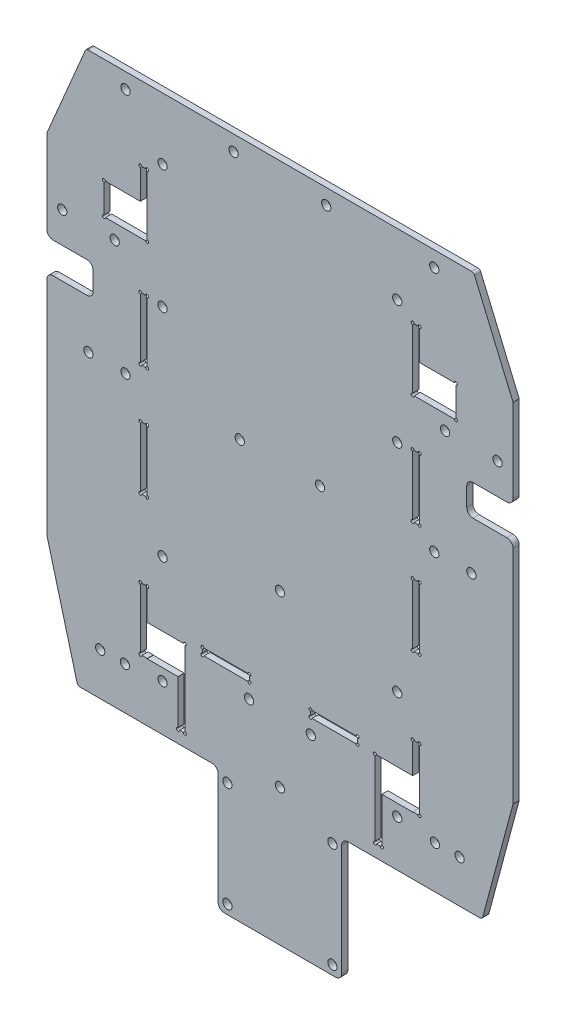
SolidWorks part; units mm, degrees
material "环氧板3240"
ref_plane "前视基准面" through (0, 0, 0) normal (0, 0, 1) x (1, 0, 0)
ref_plane "上视基准面" through (0, 0, 0) normal (0, 1, 0) x (1, 0, 0)
ref_plane "右视基准面" through (0, 0, 0) normal (1, 0, 0) x (0, 0, -1)
other "Configuration Table"
sketch "草图1" plane through (0, 0, 0) normal (0, 0, 1) x (1, 0, 0)
  line L0 (0, 90) -> (0, -90) construction
  line L2 (-43, 45.8) -> (-43, 30.5) construction
  line L3 (62.7658, 90) -> (-62.7658, 90)
  line L4 (75.5, 60) -> (75.5, -52.6795)
  line L5 (65.5, -90) -> (-65.5, -90)
  line L6 (-75.5, 60) -> (-75.5, -52.6795)
  line L7 (75.5, 90) -> (-75.5, -90) construction
  line L8 (75.5, -90) -> (-75.5, 90) construction
  line L9 (-43, 66) -> (-45.2, 66)
  line L10 (-43, 66) -> (-43, 45.8)
  line L11 (-43, 45.8) -> (-45.2, 45.8)
  line L12 (-45.2, 66) -> (-45.2, 45.8)
  line L13 (-43, 66) -> (-45.2, 45.8) construction
  line L14 (-43, 45.8) -> (-45.2, 66) construction
  line L15 (-43, 30.5) -> (-45.2, 30.5)
  line L16 (-43, 30.5) -> (-43, 10.3)
  line L17 (-43, 10.3) -> (-45.2, 10.3)
  line L18 (-45.2, 30.5) -> (-45.2, 10.3)
  line L19 (-43, 30.5) -> (-45.2, 10.3) construction
  line L20 (-43, 10.3) -> (-45.2, 30.5) construction
  line L21 (-43, -5.7) -> (-45.2, -5.7)
  line L22 (-43, -5.7) -> (-43, -25.9)
  line L23 (-43, -25.9) -> (-45.2, -25.9)
  line L24 (-45.2, -5.7) -> (-45.2, -25.9)
  line L25 (-43, -5.7) -> (-45.2, -25.9) construction
  line L26 (-43, -25.9) -> (-45.2, -5.7) construction
  line L27 (-43, 10.3) -> (-43, -5.7) construction
  line L28 (-50, 85) -> (-50, -54.1) construction
  line L33 (-50, -54.1) -> (50, -54.1) construction
  line L34 (50, -54.1) -> (50, 85) construction
  line L39 (43, -25.9) -> (45.2, -25.9)
  line L40 (45.2, -5.7) -> (45.2, -25.9)
  line L41 (43, -5.7) -> (45.2, -5.7)
  line L42 (43, -5.7) -> (43, -25.9)
  line L43 (43, 10.3) -> (45.2, 10.3)
  line L44 (45.2, 30.5) -> (45.2, 10.3)
  line L45 (43, 30.5) -> (45.2, 30.5)
  line L46 (43, 30.5) -> (43, 10.3)
  line L47 (43, 45.8) -> (45.2, 45.8)
  line L48 (45.2, 66) -> (45.2, 45.8)
  line L49 (43, 66) -> (45.2, 66)
  line L50 (43, 66) -> (43, 45.8)
  line L51 (50, 85) -> (-50, 85) construction
  line L52 (-43, -25.9) -> (-43, -50.9) construction
  line L53 (43, -71.1) -> (45.2, -71.1)
  line L54 (-43, -50.9) -> (-45.2, -50.9)
  line L55 (-43, -50.9) -> (-43, -71.1)
  line L56 (-43, -71.1) -> (-45.2, -71.1)
  line L57 (-45.2, -50.9) -> (-45.2, -71.1)
  line L58 (-43, -50.9) -> (-45.2, -71.1) construction
  line L59 (-43, -71.1) -> (-45.2, -50.9) construction
  line L60 (45.2, -50.9) -> (45.2, -71.1)
  line L61 (43, -50.9) -> (45.2, -50.9)
  line L62 (43, -50.9) -> (43, -71.1)
  line L63 (62.7658, 90) -> (75.5, 60)
  line L64 (25.1, -59) -> (9.9, -59)
  line L65 (25.1, -59) -> (25.1, -61.2)
  line L66 (25.1, -61.2) -> (9.9, -61.2)
  line L67 (9.9, -59) -> (9.9, -61.2)
  line L68 (25.1, -59) -> (9.9, -61.2) construction
  line L69 (25.1, -61.2) -> (9.9, -59) construction
  line L74 (-62.7658, 90) -> (-75.5, 60)
  line L75 (75.5, 60) -> (75.5, 90) construction
  line L76 (-9.9, -59) -> (-25.1, -59)
  line L77 (-9.9, -59) -> (-9.9, -61.2)
  line L78 (-9.9, -61.2) -> (-25.1, -61.2)
  line L79 (-25.1, -59) -> (-25.1, -61.2)
  line L80 (-9.9, -59) -> (-25.1, -61.2) construction
  line L81 (-9.9, -61.2) -> (-25.1, -59) construction
  line L82 (75.5, 90) -> (62.7658, 90) construction
  line L83 (-62.7658, 90) -> (-75.5, 90) construction
  line L84 (-75.5, 90) -> (-75.5, 60) construction
  line L85 (75.5, -52.6795) -> (65.5, -90)
  line L86 (-75.5, -52.6795) -> (-65.5, -90)
  line L87 (75.5, -52.6795) -> (75.5, -90) construction
  line L88 (75.5, -90) -> (65.5, -90) construction
  line L89 (-65.5, -90) -> (-75.5, -90) construction
  line L90 (-75.5, -90) -> (-75.5, -52.6795) construction
  circle A0 centre (50, 85) radius 1.5
  circle A1 centre (15, 85) radius 1.5
  circle A2 centre (-15, 85) radius 1.5
  circle A3 centre (-50, 85) radius 1.5
  circle A4 centre (-50, -54.1) radius 1.5 construction
  circle A5 centre (50, -54.1) radius 1.5 construction
  point P9 (0, 0)
  point P19 (-44.1, 55.9)
  point P20 (-44.1, 20.4)
  point P25 (-44.1, -15.8)
  point P34 (-44.1, -61)
  point P63 (17.5, -60.1)
  point P68 (0, -55.3627)
  point P73 (-17.5, -60.1)
  dimension "D7" = 30
  dimension "D10" = 3
  dimension "D5" = 100
  dimension "D25" = 20.2
  dimension "D1" = 180
  dimension "D2" = 20.2
  dimension "D3" = 15.3
  dimension "D4" = 2.2
  dimension "D6" = 24
  dimension "D8" = 86
  dimension "D9" = 5
  dimension "D11" = 139.1
  dimension "D12" = 25
  dimension "D13" = 20.2
  dimension "D14" = 19.8
  dimension "D15" = 15.2
  dimension "D16" = 2.2
  dimension "D17" = 149
  dimension "D18" = 151
  dimension "D19" = 16
  dimension "D20" = 23
  dimension "D21" = 30
  dimension "D22" = 10
  dimension "D23" = 15
  dimension "D24" = 20.2
extrude "凸台-拉伸1" add sketch "草图1" along normal blind 2
sketch "草图2" plane through (0, 0, 0) normal (0, 0, -1) x (-1, 0, 0)
  line L0 (0, -90) -> (0, 90) construction
  line L1 (-57, 56) -> (-43, 56)
  line L2 (-57, 56) -> (-57, 45.8)
  line L3 (-57, 45.8) -> (-43, 45.8)
  line L4 (-43, 56) -> (-43, 45.8)
  line L5 (-57, 56) -> (-43, 45.8) construction
  line L6 (-57, 45.8) -> (-43, 56) construction
  line L11 (-62.7658, 90) -> (62.7658, 90) construction
  line L12 (33, -61) -> (43, -61)
  line L13 (9.9, -61.2) -> (9.9, -59) construction
  line L15 (-50, 50.9) -> (0, 50.9) construction
  line L16 (43, -61) -> (43, -71.2)
  line L21 (43, 56) -> (43, 45.8)
  line L22 (57, 45.8) -> (43, 45.8)
  line L23 (57, 56) -> (57, 45.8)
  line L24 (57, 56) -> (43, 56)
  line L29 (33, -61) -> (33, -71.2)
  line L30 (33, -71.2) -> (43, -71.2)
  line L36 (-38, 70) -> (-38, -75) construction
  line L38 (-43, 45.8) -> (-43, 30.5) construction
  line L39 (13, 5.3) -> (-50, 5.3) construction
  line L40 (-43, 10.3) -> (-43, -5.7) construction
  line L41 (-62.7658, 90) -> (62.7658, 90) construction
  line L42 (33, -86) -> (30.8, -86)
  line L43 (-33, -61) -> (-30.8, -61)
  line L44 (-50, 5.3) -> (50, 5.3) construction
  line L45 (65.5, -90) -> (-65.5, -90) construction
  line L47 (-33, -61) -> (-43, -61)
  line L48 (-33, -61) -> (-33, -71.2)
  line L49 (-33, -71.2) -> (-43, -71.2)
  line L50 (-43, -61) -> (-43, -71.2)
  line L51 (-33, -61) -> (-43, -71.2) construction
  line L52 (-33, -71.2) -> (-43, -61) construction
  line L56 (-33, -61) -> (-33, -86)
  line L57 (-33, -86) -> (-30.8, -86)
  line L58 (-30.8, -61) -> (-30.8, -86)
  line L59 (-33, -61) -> (-30.8, -86) construction
  line L60 (-33, -86) -> (-30.8, -61) construction
  line L61 (30.8, -61) -> (30.8, -86)
  line L62 (33, -61) -> (30.8, -61)
  line L63 (33, -61) -> (33, -86)
  circle A0 centre (-38, 30) radius 1.5
  circle A1 centre (-38, -10.7) radius 1.5 construction
  circle A2 centre (-38, -40) radius 1.5
  circle A3 centre (38, -10.7) radius 1.5 construction
  circle A4 centre (38, 30) radius 1.5
  circle A5 centre (38, -40) radius 1.5
  circle A10 centre (38, -75) radius 1.5
  circle A11 centre (-38, -75) radius 1.5
  circle A12 centre (38, 70) radius 1.5
  circle A13 centre (-38, 70) radius 1.5
  circle A14 centre (-38, 5.3) radius 1.5 construction
  circle A15 centre (38, 5.3) radius 1.5 construction
  circle A16 centre (-50, 5.3) radius 1.5
  circle A17 centre (13, 5.3) radius 1.5
  circle A18 centre (-13, 5.3) radius 1.5
  circle A19 centre (50, 5.3) radius 1.5
  circle A20 centre (62, 5.3) radius 1.5
  circle A21 centre (-62, 5.3) radius 1.5
  circle A22 centre (0, -30.7) radius 1.5
  circle A23 centre (0, -85.7) radius 1.5
  circle A24 centre (0, 5.3) radius 1.5 construction
  circle A25 centre (10, -66) radius 1.5
  circle A26 centre (-10, -66) radius 1.5
  point P4 (-50, 50.9)
  point P22 (-31.9, -73.5)
  point P65 (-38, -66.1)
  point P94 (9.9, -60.1)
  dimension "D4" = 156.1
  dimension "D5" = 2.2
  dimension "D9" = 3
  dimension "D11" = 16
  dimension "D13" = 40
  dimension "D12" = 20
  dimension "D19" = 24.7
  dimension "D20" = 35
  dimension "D23" = 55
  dimension "D24" = 10
  dimension "D14" = 26
  dimension "D16" = 70
  dimension "D17" = 12
  dimension "D18" = 3
  dimension "D22" = 36
  dimension "D25" = 5.9
  dimension "D1" = 14
  dimension "D2" = 10.2
  dimension "D3" = 10
  dimension "D6" = 25
  dimension "D7" = 50
  dimension "D8" = 39.1
  dimension "D10" = 38
  dimension "D15" = 10.2
  dimension "D21" = 12
extrude "切除-拉伸1" cut sketch "草图2" against normal through all
sketch "草图3" plane through (0, 0, 0) normal (0, 0, -1) x (-1, 0, 0)
  line L0 (-44.1, 66) -> (-44.1, 45.8) construction
  line L1 (-45.2, 66) -> (-43, 66) construction
  line L2 (-43, 45.8) -> (-57, 45.8) construction
  line L3 (0, 90) -> (0, -90) construction
  line L4 (-62.7658, 90) -> (62.7658, 90) construction
  line L5 (65.5, -90) -> (-65.5, -90) construction
  line L6 (44.1, 66) -> (44.1, 45.8) construction
  circle A0 centre (-57, 56) radius 0.5
  circle A1 centre (-57, 45.8) radius 0.5
  circle A4 centre (-45.2, 66) radius 0.5
  circle A6 centre (-43, 45.8) radius 0.5
  circle A7 centre (-45.2, 30.5) radius 0.5
  circle A8 centre (-45.2, 10.3) radius 0.5
  circle A9 centre (-45.2, -5.7) radius 0.5
  circle A10 centre (-45.2, -25.9) radius 0.5
  circle A11 centre (-45.2, -50.9) radius 0.5
  circle A13 centre (-45.2, -71.1) radius 0.5
  circle A14 centre (-30.8, -61) radius 0.5
  circle A15 centre (-33, -86) radius 0.5
  circle A16 centre (-43, -50.9) radius 0.5
  circle A17 centre (-43, -25.9) radius 0.5
  circle A18 centre (-43, -5.7) radius 0.5
  circle A19 centre (-43, 10.3) radius 0.5
  circle A20 centre (-43, 30.5) radius 0.5
  circle A21 centre (-43, 66) radius 0.5
  circle A22 centre (-30.8, -86) radius 0.5
  circle A23 centre (-25.1, -59) radius 0.5
  circle A24 centre (-25.1, -61.2) radius 0.5
  circle A25 centre (-9.9, -61.2) radius 0.5
  circle A26 centre (-9.9, -59) radius 0.5
  circle A27 centre (9.9, -59) radius 0.5
  circle A28 centre (9.9, -61.2) radius 0.5
  circle A29 centre (25.1, -61.2) radius 0.5
  circle A30 centre (25.1, -59) radius 0.5
  circle A31 centre (30.8, -86) radius 0.5
  circle A32 centre (43, 66) radius 0.5
  circle A33 centre (43, 30.5) radius 0.5
  circle A34 centre (43, 10.3) radius 0.5
  circle A35 centre (43, -5.7) radius 0.5
  circle A36 centre (43, -25.9) radius 0.5
  circle A37 centre (43, -50.9) radius 0.5
  circle A38 centre (33, -86) radius 0.5
  circle A39 centre (30.8, -61) radius 0.5
  circle A40 centre (45.2, -71.1) radius 0.5
  circle A41 centre (45.2, -50.9) radius 0.5
  circle A42 centre (45.2, -25.9) radius 0.5
  circle A43 centre (45.2, -5.7) radius 0.5
  circle A44 centre (45.2, 10.3) radius 0.5
  circle A45 centre (45.2, 30.5) radius 0.5
  circle A46 centre (43, 45.8) radius 0.5
  circle A47 centre (45.2, 66) radius 0.5
  circle A48 centre (57, 45.8) radius 0.5
  circle A49 centre (57, 56) radius 0.5
  dimension "D1" = 1
extrude "切除-拉伸2" cut sketch "草图3" against normal through all
sketch "草图4" plane through (0, 0, 0) normal (0, 0, -1) x (-1, 0, 0)
  line L0 (-69.1977, -76.2) -> (-52.0554, -76.2) construction
  line L1 (-65.5, -90) -> (-75.5, -52.6795) construction
  line L2 (65.5, -90) -> (-65.5, -90) construction
  line L3 (0, -90) -> (0, -83.7521) construction
  circle A0 centre (-58.2, -76.2) radius 1.5
  circle A1 centre (-50.2, -76.2) radius 1.5
  circle A2 centre (58.2, -76.2) radius 1.5
  circle A3 centre (50.2, -76.2) radius 1.5
  dimension "D1" = 3
  dimension "D4" = 8
  dimension "D2" = 13.8
  dimension "D3" = 7.3
extrude "切除-拉伸3" cut sketch "草图4" against normal blind 5
sketch "草图5" plane through (0, 0, 0) normal (0, 0, -1) x (-1, 0, 0)
  line L0 (-75.5, 41) -> (-45.5988, 41) construction
  line L1 (-75.5, -52.6795) -> (-75.5, 60) construction
  line L2 (-62.7658, 90) -> (62.7658, 90) construction
  line L3 (0, 90) -> (0, 0) construction
  circle A0 centre (-53.5, 41) radius 1.5
  circle A1 centre (-70.5, 41) radius 1.5
  circle A2 centre (53.5, 41) radius 1.5
  circle A3 centre (70.5, 41) radius 1.5
  dimension "D1" = 3
  dimension "D2" = 17
  dimension "D3" = 22
  dimension "D4" = 49
extrude "切除-拉伸4" cut sketch "草图5" against normal blind 2
fillet "圆角1" radius 1 4 edges at (65.5, -90, 1) (-65.5, -90, 1) (-62.7658, 90, 1) (62.7658, 90, 1)
sketch "草图6" plane through (0, 0, 2) normal (0, 0, 1) x (1, 0, 0)
  line L0 (-75.5, 60) -> (-75.5, -52.6795) construction
  line L1 (-75.5, 31) -> (-60.5, 31)
  line L2 (-75.5, 31) -> (-75.5, 21)
  line L3 (-75.5, 21) -> (-60.5, 21)
  line L4 (-60.5, 31) -> (-60.5, 21)
  line L5 (0, 90) -> (0, -2.9744) construction
  line L6 (62.1039, 90) -> (-62.1039, 90) construction
  line L7 (75.5, 21) -> (60.5, 21)
  line L8 (60.5, 31) -> (60.5, 21)
  line L9 (75.5, 31) -> (60.5, 31)
  line L10 (75.5, 31) -> (75.5, 21)
  circle A0 centre (-70.5, 41) radius 1.5 construction
  dimension "D1" = 10
  dimension "D2" = 10
  dimension "D3" = 15
extrude "切除-拉伸5" cut sketch "草图6" against normal blind 10
fillet "圆角2" radius 2 8 edges at (-60.5, 21, 1) (-60.5, 31, 1) (60.5, 21, 1) (60.5, 31, 1) (75.5, 21, 1) (75.5, 31, 1) (-75.5, 21, 1) (-75.5, 31, 1)
sketch "草图7" plane through (0, 0, 2) normal (0, 0, 1) x (1, 0, 0)
  line L0 (-64.7327, -90) -> (64.7327, -90) construction
  line L1 (-20, -90) -> (20, -90)
  line L2 (-20, -90) -> (-20, -130)
  line L3 (-20, -130) -> (20, -130)
  line L4 (20, -90) -> (20, -130)
  line L5 (0, -130) -> (0, 0) construction
  line L6 (-17, -93) -> (-17, -127) construction
  circle A0 centre (-17, -93) radius 1.5
  circle A1 centre (17, -93) radius 1.5
  circle A2 centre (-17, -127) radius 1.5
  circle A3 centre (17, -127) radius 1.5
  dimension "D3" = 3
  dimension "D4" = 3
  dimension "D5" = 3
  dimension "D1" = 40
  dimension "D2" = 40
  dimension "D6" = 3
extrude "凸台-拉伸2" add sketch "草图7" against normal blind 2
fillet "圆角3" radius 2 4 edges at (20, -90, 1) (20, -130, 1) (-20, -130, 1) (-20, -90, 1)
